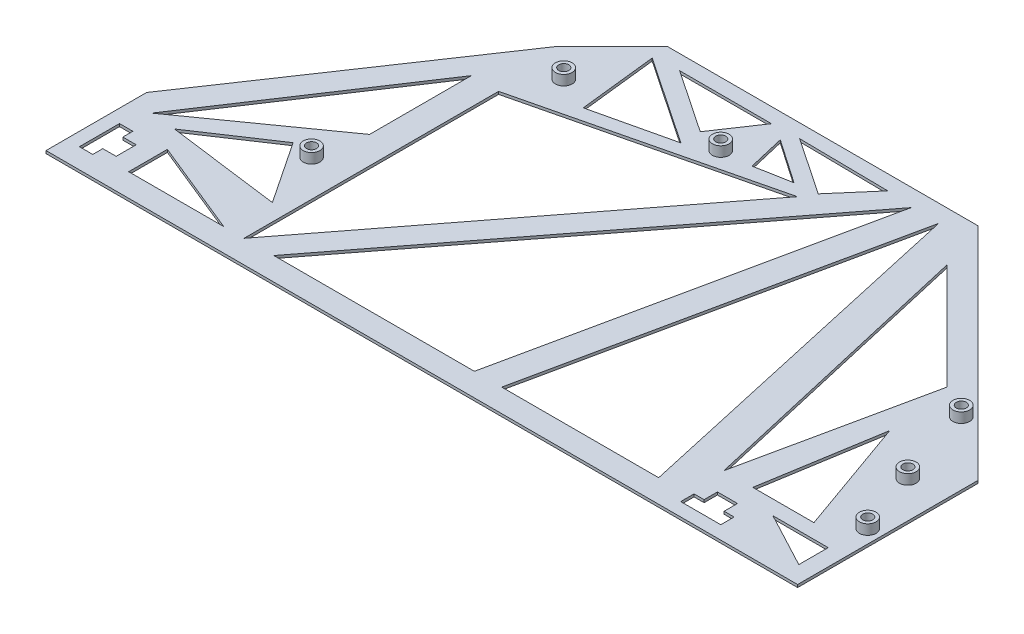
SolidWorks part; units mm, degrees
ref_plane "Front Plane" through (0, 0, 0) normal (0, 0, 1) x (1, 0, 0)
ref_plane "Top Plane" through (0, 0, 0) normal (0, 1, 0) x (1, 0, 0)
ref_plane "Right Plane" through (0, 0, 0) normal (1, 0, 0) x (0, 0, -1)
sketch "Sketch2" plane through (0, 0, 0) normal (0, 1, 0) x (1, 0, 0)
  circle A0 centre (41.5, 38) radius 2.5
  circle A1 centre (59, 96) radius 2.5
  circle A2 centre (101, 101) radius 2.5
  circle A3 centre (206, 68) radius 2.5
  circle A4 centre (214, 44) radius 2.5
  circle A5 centre (221, 25) radius 2.5
extrude "Boss-Extrude1" add sketch "Sketch2" along normal blind 3 contours A2 | A3 | A4 | A5 | A0 | A1
sketch "Sketch4" plane through (0, 0, 0) normal (0, 1, 0) x (1, 0, 0)
  line L1 (0, 0) -> (225, 0)
  line L2 (0, 0) -> (0, 120)
  line L3 (0, 120) -> (225, 120)
  line L4 (225, 0) -> (225, 120)
  circle A2 centre (221, 25) radius 2.5 construction
  dimension "D1" = 120
  dimension "D2" = 4
  dimension "D3" = 225
extrude "Boss-Extrude2" add sketch "Sketch4" against normal blind 0.8
sketch "Sketch9" plane through (0, 3, 0) normal (0, 1, 0) x (1, 0, 0)
  point P0 (59, 96)
  point P3 (101, 101)
  point P6 (206, 68)
  point P9 (214, 44)
  point P12 (221, 25)
  point P15 (41.5, 38)
sketch "Sketch14" plane through (0, 3, 0) normal (0, 1, 0) x (1, 0, 0)
  point P0 (59, 96)
  point P4 (101, 101)
  point P7 (206, 68)
  point P10 (214, 44)
  point P13 (221, 25)
  point P16 (41.5, 38)
sketch "Sketch17" plane through (0, 3, 0) normal (0, 1, 0) x (1, 0, 0)
  point P0 (59, 96)
sketch "Sketch22" plane through (0, 3, 0) normal (0, 1, 0) x (1, 0, 0)
  point P0 (59, 96)
  point P3 (101, 101)
  point P6 (206, 68)
  point P9 (214, 44)
  point P12 (221, 25)
  point P15 (41.5, 38)
hole_wizard "Ø3.0mm Dowel Hole1" positions "Sketch22" profile "Sketch21" hole size "Ø3.0" standard "ANSI Metric"
sketch "Sketch21" plane through (59, 3, -96) normal (1, 0, 0) x (0, 0, 1)
  line L0 (0, 0) -> (0, 4)
  line L1 (0, 4) -> (1.5, 4)
  line L2 (1.5, 4) -> (1.5, 0)
  line L5 (1.5, 0) -> (0, 0)
  line L10 (0, 4) -> (-1.5, 4) construction
  line L11 (0, -6.35) -> (0, 107.95) construction
  dimension "Hole Dia." = 3
  dimension "Hole Depth" = 4
  dimension "Drill Angle" = 180
sketch "Sketch27" plane through (0, 0, 0) normal (0, 1, 0) x (1, 0, 0)
  line L1 (186, 8) -> (189, 8)
  line L2 (186, 8) -> (186, 4)
  line L3 (186, 4) -> (198, 4)
  line L4 (198, 8) -> (198, 4)
  line L5 (0, 0) -> (225, 0) construction
  line L6 (225, 0) -> (225, 120) construction
  line L9 (195, 8) -> (198, 8)
  line L11 (189, 8) -> (189, 12)
  line L12 (189, 12) -> (195, 12)
  line L13 (195, 8) -> (195, 12)
  line L14 (0, 120) -> (0, 0) construction
  line L15 (4, 6) -> (8, 6)
  line L16 (4, 6) -> (4, 18)
  line L17 (4, 18) -> (8, 18)
  line L18 (8, 6) -> (8, 9)
  line L19 (8, 15) -> (8, 18)
  line L20 (8, 15) -> (12, 15)
  line L22 (8, 9) -> (12, 9)
  line L23 (12, 15) -> (12, 9)
  dimension "D1" = 4
  dimension "D2" = 27
  dimension "D3" = 12
  dimension "D4" = 4
  dimension "D5" = 4
  dimension "D6" = 3
  dimension "D7" = 3
  dimension "D8" = 6
  dimension "D9" = 4
  dimension "D10" = 12
  dimension "D11" = 4
  dimension "D12" = 4
  dimension "D13" = 3
  dimension "D14" = 3
extrude "Cut-Extrude1" cut sketch "Sketch27" against normal up to next
chamfer "Chamfer1" distance 66 angle 45 2 edges at (0, -0.4, -120) (225, -0.4, -120)
sketch "Sketch28" plane through (0, 0, 0) normal (0, 1, 0) x (1, 0, 0)
  line L0 (52.3883, 6.8919) -> (52.3883, 83.0936)
  line L1 (52.3883, 83.0936) -> (124.428, 100.5149)
  line L2 (124.428, 100.5149) -> (52.3883, 6.8919)
  line L3 (144.2867, 114.7244) -> (61.3133, 6.8919)
  line L4 (61.3133, 6.8919) -> (121.3387, 6.8919)
  line L5 (121.3387, 6.8919) -> (144.2867, 114.7244)
  line L6 (152.4858, 114.7244) -> (129.5379, 6.8919)
  line L7 (129.5379, 6.8919) -> (176.5153, 6.8919)
  line L8 (176.5153, 6.8919) -> (152.4858, 114.7244)
  line L9 (164.5006, 105.1957) -> (196.1719, 73.5243)
  line L10 (196.1719, 73.5243) -> (184.4576, 18.4785)
  line L11 (184.4576, 18.4785) -> (164.5006, 105.1957)
  line L12 (198.8883, 53.7034) -> (211.4059, 18.4785)
  line L13 (211.4059, 18.4785) -> (193.1109, 18.4785)
  line L14 (193.1109, 18.4785) -> (198.8883, 53.7034)
  line L15 (44.2427, 83.0936) -> (44.2427, 52.6161)
  line L16 (44.2427, 52.6161) -> (6.0824, 25.5061)
  line L17 (6.0824, 25.5061) -> (44.2427, 83.0936)
  line L18 (13.6306, 24.8195) -> (34.9442, 39.0302)
  line L19 (34.9442, 39.0302) -> (47.3596, 20.4091)
  line L20 (47.3596, 20.4091) -> (13.6306, 24.8195)
  line L21 (17.8584, 18.4785) -> (17.8584, 6.8919)
  line L22 (17.8584, 6.8919) -> (46.339, 6.8919)
  line L23 (46.339, 6.8919) -> (17.8584, 18.4785)
  line L24 (66.7416, 114.7244) -> (69.3393, 91.4875)
  line L25 (69.3393, 91.4875) -> (93.0434, 97.0076)
  line L26 (93.0434, 97.0076) -> (66.7416, 114.7244)
  line L27 (74.1342, 115.5508) -> (93.0434, 102.8137)
  line L28 (93.0434, 102.8137) -> (101.6231, 115.5508)
  line L29 (101.6231, 115.5508) -> (74.1342, 115.5508)
  line L30 (136.4468, 115.5508) -> (126.8136, 104.3678)
  line L31 (126.8136, 104.3678) -> (109.7107, 115.8882)
  line L32 (109.7107, 115.8882) -> (136.4468, 115.5508)
  line L33 (107.1143, 112.7021) -> (120.3193, 103.6101)
  line L34 (120.3193, 103.6101) -> (109.7107, 101.6532)
  line L35 (109.7107, 101.6532) -> (107.1143, 112.7021)
  line L36 (203.4566, 14.1415) -> (220.0186, 14.1415)
  line L37 (220.0186, 14.1415) -> (220.0186, 5.3365)
  line L38 (220.0186, 5.3365) -> (203.4566, 14.1415)
extrude "Cut-Extrude2" cut sketch "Sketch28" against normal up to next
chamfer "Chamfer3" distance 70 angle 11 1 edges at (0, -0.4, -54)
